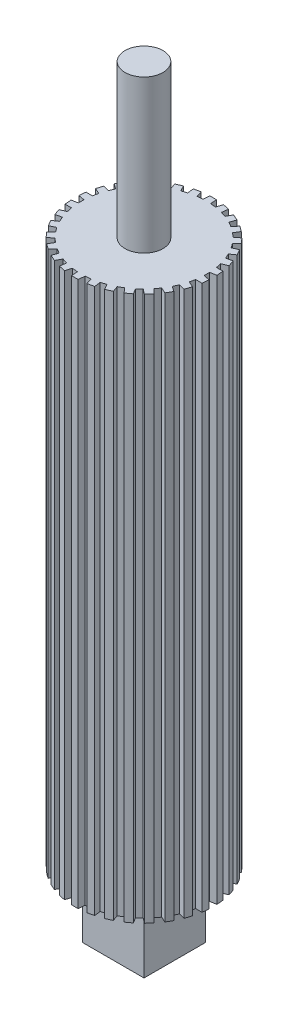
SolidWorks part; units mm, degrees
ref_plane "Front Plane" through (0, 0, 0) normal (0, 0, 1) x (1, 0, 0)
ref_plane "Top Plane" through (0, 0, 0) normal (0, 1, 0) x (1, 0, 0)
ref_plane "Right Plane" through (0, 0, 0) normal (1, 0, 0) x (0, 0, -1)
sketch "Sketch2" plane through (0, 0, 0) normal (0, 1, 0) x (1, 0, 0)
  line L1 (-0.7753, 12.6763) -> (-0.6703, 13.9539)
  line L2 (0.7753, 12.6763) -> (0.6703, 13.9539)
  line L3 (1.8772, 12.5605) -> (2.2456, 13.7883)
  line L4 (3.3939, 12.2381) -> (3.5568, 13.5096)
  line L5 (4.4476, 11.8957) -> (5.0633, 13.0201)
  line L6 (5.8642, 11.265) -> (6.2879, 12.4749)
  line L7 (6.8237, 10.7111) -> (7.6597, 11.6829)
  line L8 (8.0782, 9.7996) -> (8.7442, 10.895)
  line L9 (8.9015, 9.0583) -> (9.9213, 9.8351)
  line L10 (9.9391, 7.9059) -> (10.8183, 8.8389)
  line L11 (10.5903, 7.0096) -> (11.7493, 7.5574)
  line L12 (11.3657, 5.6667) -> (12.4196, 6.3965)
  line L13 (11.8163, 4.6546) -> (13.0638, 4.9494)
  line L14 (12.2955, 3.1798) -> (13.4781, 3.6745)
  line L15 (12.5258, 2.0961) -> (13.8074, 2.1252)
  line L16 (12.6879, 0.554) -> (13.9475, 0.792)
  line L17 (12.6879, -0.554) -> (13.9475, -0.792)
  line L18 (12.5258, -2.0961) -> (13.8074, -2.1252)
  line L19 (12.2955, -3.1798) -> (13.4781, -3.6745)
  line L20 (11.8163, -4.6546) -> (13.0638, -4.9494)
  line L21 (11.3657, -5.6667) -> (12.4196, -6.3965)
  line L22 (10.5903, -7.0096) -> (11.7493, -7.5574)
  line L23 (9.9391, -7.9059) -> (10.8183, -8.8389)
  line L24 (8.9015, -9.0583) -> (9.9213, -9.8351)
  line L25 (8.0782, -9.7996) -> (8.7442, -10.895)
  line L26 (6.8237, -10.7111) -> (7.6597, -11.6829)
  line L27 (5.8642, -11.265) -> (6.2879, -12.4749)
  line L28 (4.4476, -11.8957) -> (5.0633, -13.0201)
  line L29 (3.3939, -12.2381) -> (3.5568, -13.5096)
  line L30 (1.8772, -12.5605) -> (2.2456, -13.7883)
  line L31 (0.7753, -12.6763) -> (0.6703, -13.9539)
  line L32 (-0.7753, -12.6763) -> (-0.6703, -13.9539)
  line L33 (-1.8772, -12.5605) -> (-2.2456, -13.7883)
  line L34 (-3.3939, -12.2381) -> (-3.5568, -13.5096)
  line L35 (-4.4476, -11.8957) -> (-5.0633, -13.0201)
  line L36 (-5.8642, -11.265) -> (-6.2879, -12.4749)
  line L37 (-6.8237, -10.7111) -> (-7.6597, -11.6829)
  line L38 (-8.0782, -9.7996) -> (-8.7442, -10.895)
  line L39 (-8.9015, -9.0583) -> (-9.9213, -9.8351)
  line L40 (-9.9391, -7.9059) -> (-10.8183, -8.8389)
  line L41 (-10.5903, -7.0096) -> (-11.7493, -7.5574)
  line L42 (-11.3657, -5.6667) -> (-12.4196, -6.3965)
  line L43 (-11.8163, -4.6546) -> (-13.0638, -4.9494)
  line L44 (-12.2955, -3.1798) -> (-13.4781, -3.6745)
  line L45 (-12.5258, -2.0961) -> (-13.8074, -2.1252)
  line L46 (-12.6879, -0.554) -> (-13.9475, -0.792)
  line L47 (-12.6879, 0.554) -> (-13.9475, 0.792)
  line L48 (-12.5258, 2.0961) -> (-13.8074, 2.1252)
  line L49 (-12.2955, 3.1798) -> (-13.4781, 3.6745)
  line L50 (-11.8163, 4.6546) -> (-13.0638, 4.9494)
  line L51 (-11.3657, 5.6667) -> (-12.4196, 6.3965)
  line L52 (-10.5903, 7.0096) -> (-11.7493, 7.5574)
  line L53 (-9.9391, 7.9059) -> (-10.8183, 8.8389)
  line L54 (-8.9015, 9.0583) -> (-9.9213, 9.8351)
  line L55 (-8.0782, 9.7996) -> (-8.7442, 10.895)
  line L56 (-6.8237, 10.7111) -> (-7.6597, 11.6829)
  line L57 (-5.8642, 11.265) -> (-6.2879, 12.4749)
  line L58 (-4.4476, 11.8957) -> (-5.0633, 13.0201)
  line L59 (-3.3939, 12.2381) -> (-3.5568, 13.5096)
  line L60 (-1.8772, 12.5605) -> (-2.2456, 13.7883)
  arc A0 (-2.2456, 13.7883) -> (-3.5568, 13.5096) centre (0, 0) ccw
  arc A1 (-0.7753, 12.6763) -> (-1.8772, 12.5605) centre (0, 0) ccw
  arc A3 (-3.3939, 12.2381) -> (-4.4476, 11.8957) centre (0, 0) ccw
  arc A4 (-5.0633, 13.0201) -> (-6.2879, 12.4749) centre (0, 0) ccw
  arc A5 (-5.8642, 11.265) -> (-6.8237, 10.7111) centre (0, 0) ccw
  arc A6 (-7.6597, 11.6829) -> (-8.7442, 10.895) centre (0, 0) ccw
  arc A7 (-8.0782, 9.7996) -> (-8.9015, 9.0583) centre (0, 0) ccw
  arc A8 (-9.9213, 9.8351) -> (-10.8183, 8.8389) centre (0, 0) ccw
  arc A9 (-9.9391, 7.9059) -> (-10.5903, 7.0096) centre (0, 0) ccw
  arc A10 (-11.7493, 7.5574) -> (-12.4196, 6.3965) centre (0, 0) ccw
  arc A11 (-11.3657, 5.6667) -> (-11.8163, 4.6546) centre (0, 0) ccw
  arc A12 (-13.0638, 4.9494) -> (-13.4781, 3.6745) centre (0, 0) ccw
  arc A13 (-12.2955, 3.1798) -> (-12.5258, 2.0961) centre (0, 0) ccw
  arc A14 (-13.8074, 2.1252) -> (-13.9475, 0.792) centre (0, 0) ccw
  arc A15 (-12.6879, 0.554) -> (-12.6879, -0.554) centre (0, 0) ccw
  arc A16 (-13.9475, -0.792) -> (-13.8074, -2.1252) centre (0, 0) ccw
  arc A17 (-12.5258, -2.0961) -> (-12.2955, -3.1798) centre (0, 0) ccw
  arc A18 (-13.4781, -3.6745) -> (-13.0638, -4.9494) centre (0, 0) ccw
  arc A19 (-11.8163, -4.6546) -> (-11.3657, -5.6667) centre (0, 0) ccw
  arc A20 (-12.4196, -6.3965) -> (-11.7493, -7.5574) centre (0, 0) ccw
  arc A21 (-10.5903, -7.0096) -> (-9.9391, -7.9059) centre (0, 0) ccw
  arc A22 (-10.8183, -8.8389) -> (-9.9213, -9.8351) centre (0, 0) ccw
  arc A23 (-8.9015, -9.0583) -> (-8.0782, -9.7996) centre (0, 0) ccw
  arc A24 (-8.7442, -10.895) -> (-7.6597, -11.6829) centre (0, 0) ccw
  arc A25 (-6.8237, -10.7111) -> (-5.8642, -11.265) centre (0, 0) ccw
  arc A26 (-6.2879, -12.4749) -> (-5.0633, -13.0201) centre (0, 0) ccw
  arc A27 (-4.4476, -11.8957) -> (-3.3939, -12.2381) centre (0, 0) ccw
  arc A28 (-3.5568, -13.5096) -> (-2.2456, -13.7883) centre (0, 0) ccw
  arc A29 (-1.8772, -12.5605) -> (-0.7753, -12.6763) centre (0, 0) ccw
  arc A30 (-0.6703, -13.9539) -> (0.6703, -13.9539) centre (0, 0) ccw
  arc A31 (0.7753, -12.6763) -> (1.8772, -12.5605) centre (0, 0) ccw
  arc A32 (2.2456, -13.7883) -> (3.5568, -13.5096) centre (0, 0) ccw
  arc A33 (3.3939, -12.2381) -> (4.4476, -11.8957) centre (0, 0) ccw
  arc A34 (5.0633, -13.0201) -> (6.2879, -12.4749) centre (0, 0) ccw
  arc A35 (5.8642, -11.265) -> (6.8237, -10.7111) centre (0, 0) ccw
  arc A36 (7.6597, -11.6829) -> (8.7442, -10.895) centre (0, 0) ccw
  arc A37 (8.0782, -9.7996) -> (8.9015, -9.0583) centre (0, 0) ccw
  arc A38 (9.9213, -9.8351) -> (10.8183, -8.8389) centre (0, 0) ccw
  arc A39 (9.9391, -7.9059) -> (10.5903, -7.0096) centre (0, 0) ccw
  arc A40 (11.7493, -7.5574) -> (12.4196, -6.3965) centre (0, 0) ccw
  arc A41 (11.3657, -5.6667) -> (11.8163, -4.6546) centre (0, 0) ccw
  arc A42 (13.0638, -4.9494) -> (13.4781, -3.6745) centre (0, 0) ccw
  arc A43 (12.2955, -3.1798) -> (12.5258, -2.0961) centre (0, 0) ccw
  arc A44 (13.8074, -2.1252) -> (13.9475, -0.792) centre (0, 0) ccw
  arc A45 (12.6879, -0.554) -> (12.6879, 0.554) centre (0, 0) ccw
  arc A46 (13.9475, 0.792) -> (13.8074, 2.1252) centre (0, 0) ccw
  arc A47 (12.5258, 2.0961) -> (12.2955, 3.1798) centre (0, 0) ccw
  arc A48 (13.4781, 3.6745) -> (13.0638, 4.9494) centre (0, 0) ccw
  arc A49 (0.6703, 13.9539) -> (-0.6703, 13.9539) centre (0, 0) ccw
  arc A50 (3.5568, 13.5096) -> (2.2456, 13.7883) centre (0, 0) ccw
  arc A51 (6.2879, 12.4749) -> (5.0633, 13.0201) centre (0, 0) ccw
  arc A52 (8.7442, 10.895) -> (7.6597, 11.6829) centre (0, 0) ccw
  arc A53 (1.8772, 12.5605) -> (0.7753, 12.6763) centre (0, 0) ccw
  arc A54 (4.4476, 11.8957) -> (3.3939, 12.2381) centre (0, 0) ccw
  arc A55 (6.8237, 10.7111) -> (5.8642, 11.265) centre (0, 0) ccw
  arc A56 (8.9015, 9.0583) -> (8.0782, 9.7996) centre (0, 0) ccw
  arc A57 (10.5903, 7.0096) -> (9.9391, 7.9059) centre (0, 0) ccw
  arc A58 (10.8183, 8.8389) -> (9.9213, 9.8351) centre (0, 0) ccw
  arc A59 (12.4196, 6.3965) -> (11.7493, 7.5574) centre (0, 0) ccw
  arc A60 (11.8163, 4.6546) -> (11.3657, 5.6667) centre (0, 0) ccw
  point P129 (0, 0)
  dimension "D1" = 30
extrude "Boss-Extrude1" add sketch "Sketch2" along normal blind 211.1375 contours L39 A22 L40 A21 L41 A20 L42 A19 L43 A18 L44 A17 L45 A16 L46 A15 L47 A14 L48 A13 L49 A12 L50 A11 L51 A10 L52 A9 L53 A8 L54 A7 L55 A6 L56 A5 L57 A4 L58 A3 L59 A0 L60 A1 L1 A49 L2 A53 L3 A50 L4 A54 L5 A51 L6 A55 L7 A52 L8 A56 L9 A58 L10 A57 L11 A59 L12 A60 L13 A48 L14 A47 L15 A46 L16 A45 L17 A44 L18 A43 L19 A42 L20 A41 L21 A40 L22 A39 L23 A38 L24 A37 L25 A36 L26 A35 L27 A34 L28 A33 L29 A32 L30 A31 L31 A30 L32 A29 L33 A28 L34 A27 L35 A26 L36 A25 L37 A24 L38 A23
scale "Scale2" scale about centroid uniform scaling no x scale factor 0.96 y scale factor 1 z scale factor 0.96
sketch "Sketch3" plane through (0, 211.1375, 0) normal (0, 1, 0) x (1, 0, 0)
  circle A0 centre (0, 0) radius 3.6805
  dimension "D1" = 7.3609
extrude "Boss-Extrude2" add sketch "Sketch3" along normal blind 29.5593
sketch "Sketch4" plane through (0, 0, 0) normal (0, -1, 0) x (-1, 0, 0)
  circle A0 centre (0, 0) radius 3.6805
  dimension "D1" = 7.3609
extrude "Boss-Extrude3" add sketch "Sketch4" along normal blind 29.5593
sketch "Sketch5" plane through (0, -29.5593, 0) normal (0, -1, 0) x (1, 0, 0)
  circle A0 centre (0, 0) radius 17.9594
extrude "Cut-Extrude1" cut sketch "Sketch5" against normal blind 135.128
sketch "Sketch6" plane through (0, 105.5687, 0) normal (0, -1, 0) x (1, 0, 0)
  line L1 (-5.969, -5.969) -> (5.969, -5.969)
  line L2 (-5.969, -5.969) -> (-5.969, 5.969)
  line L3 (-5.969, 5.969) -> (5.969, 5.969)
  line L4 (5.969, -5.969) -> (5.969, 5.969)
  line L5 (-5.969, -5.969) -> (5.969, 5.969) construction
  line L6 (-5.969, 5.969) -> (5.969, -5.969) construction
  point P0 (0, 0)
  dimension "D1" = 11.938
  dimension "D2" = 11.938
extrude "Boss-Extrude4" add sketch "Sketch6" along normal blind 12.7 contours L3 L4 L1 L2
